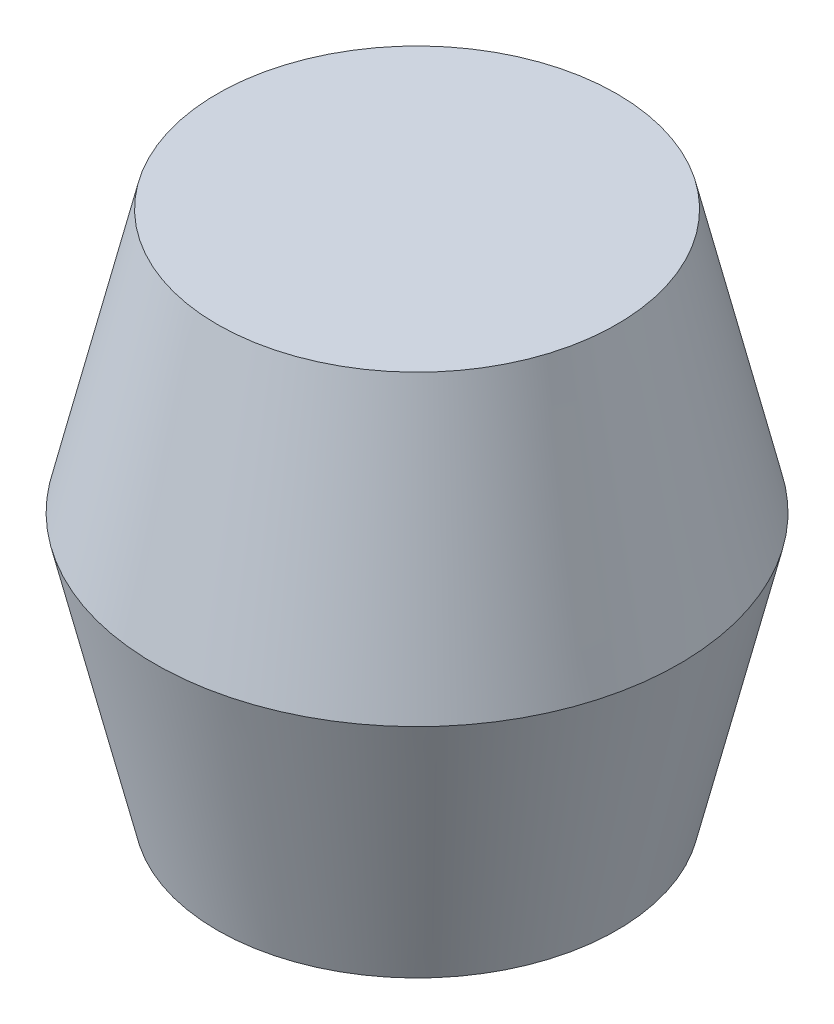
SolidWorks part; units mm, degrees
ref_plane "Front Plane" through (0, 0, 0) normal (0, 0, 1) x (1, 0, 0)
ref_plane "Top Plane" through (0, 0, 0) normal (0, 1, 0) x (1, 0, 0)
ref_plane "Right Plane" through (0, 0, 0) normal (1, 0, 0) x (0, 0, -1)
sketch "Sketch1" plane through (0, 0, 0) normal (1, 0, 0) x (0, 0, -1)
  line L0 (0, 0) -> (0, 56.3896) construction
  line L1 (0, 6.35) -> (1.1811, 6.35)
  line L2 (1.1811, 6.35) -> (1.1811, 0)
  line L3 (1.1811, 0) -> (3.0226, 0)
  line L4 (3.0226, 0) -> (3.9688, 3.9624)
  line L5 (3.9688, 3.9624) -> (3.0226, 7.9375)
  line L6 (3.0226, 7.9375) -> (0, 7.9375)
  line L7 (0, 7.9375) -> (0, 6.35)
  dimension "D1" = 6.0452
  dimension "D2" = 7.9375
  dimension "D3" = 3.9624
  dimension "D4" = 7.9375
  dimension "D5" = 2.3622
  dimension "D6" = 6.35
  dimension "D7" = 6.0452
revolve "Revolve1" add sketch "Sketch1" angle 360 about L0
